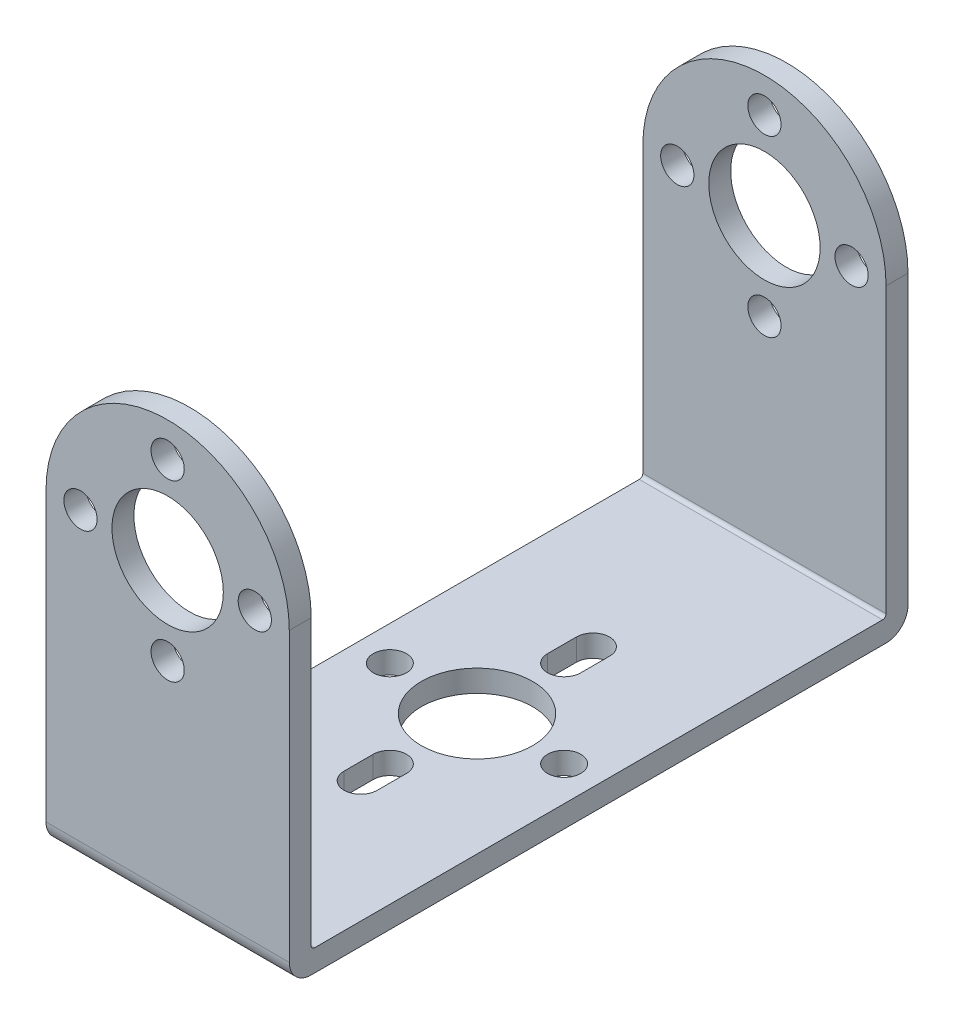
SolidWorks part; units mm, degrees
ref_plane "Front Plane" through (0, 0, 0) normal (0, 0, 1) x (1, 0, 0)
ref_plane "Top Plane" through (0, 0, 0) normal (0, 1, 0) x (1, 0, 0)
ref_plane "Right Plane" through (0, 0, 0) normal (1, 0, 0) x (0, 0, -1)
sketch "Sketch1" plane through (0, 0, 0) normal (1, 0, 0) x (0, 0, -1)
  line L1 (0, 0) -> (44.45, 0)
  line L2 (0, 0) -> (0, 30.9626)
  line L3 (0, 30.9626) -> (44.45, 30.9626)
  line L4 (44.45, 0) -> (44.45, 30.9626)
  dimension "D1" = 30.9626
  dimension "D2" = 44.45
extrude "Extrude1" add sketch "Sketch1" along normal blind 17.4752
sketch "Sketch2" plane through (17.4752, 0, 0) normal (1, 0, 0) x (0, 0, -1)
  line L0 (44.45, 30.9626) -> (0, 30.9626) construction
  line L1 (1.5748, 30.9626) -> (42.8752, 30.9626)
  line L2 (1.5748, 30.9626) -> (1.5748, 1.5748)
  line L3 (1.5748, 1.5748) -> (42.8752, 1.5748)
  line L4 (42.8752, 30.9626) -> (42.8752, 1.5748)
  line L5 (44.45, 0) -> (44.45, 30.9626) construction
  line L6 (0, 0) -> (44.45, 0) construction
  line L7 (0, 30.9626) -> (0, 0) construction
  dimension "D1" = 1.5748
  dimension "D2" = 1.5748
  dimension "D3" = 1.5748
extrude "Extrude2" cut sketch "Sketch2" against normal up to surface (17.4752 mm away) up to face at (0, 15.4813, -22.225)
sketch "Sketch3" plane through (0, 0, 0) normal (0, 0, 1) x (1, 0, 0)
  line L0 (17.4752, 30.9626) -> (0, 30.9626) construction
  line L1 (0, 22.225) -> (0, 0)
  line L2 (0, 0) -> (17.4752, 0)
  line L3 (17.4752, 0) -> (17.4752, 22.225)
  arc A0 (17.4752, 22.225) -> (0, 22.225) centre (8.7376, 22.225) ccw
extrude "Extrude3" cut sketch "Sketch3" against normal through all flip side to cut
sketch "Sketch4" plane through (0, 0, 0) normal (0, 0, 1) x (1, 0, 0)
  circle A0 centre (8.7376, 22.225) radius 4.0005
  circle A1 centre (8.7376, 22.225) radius 6.2611 construction
  circle A2 centre (2.4765, 22.225) radius 1.1938
  circle A3 centre (14.9987, 22.225) radius 1.1938
  circle A4 centre (8.7376, 15.9639) radius 1.1938
  circle A5 centre (8.7376, 28.4861) radius 1.1938
  dimension "D1" = 12.5222
extrude "Extrude4" cut sketch "Sketch4" against normal through all
sketch "Sketch5" plane through (0, 1.5748, 0) normal (0, 1, 0) x (1, 0, 0)
  line L0 (0, 22.225) -> (17.4752, 22.225) construction
  line L1 (0, 1.5748) -> (0, 42.8752) construction
  line L2 (17.4752, 1.5748) -> (17.4752, 42.8752) construction
  line L4 (17.4752, 44.45) -> (0, 44.45) construction
  line L5 (9.9314, 30.5562) -> (9.9314, 28.4861)
  line L6 (7.5438, 30.5562) -> (7.5438, 28.4861)
  line L7 (7.5438, 15.9639) -> (7.5438, 13.8684)
  line L8 (9.9314, 15.9639) -> (9.9314, 13.8684)
  circle A0 centre (8.7376, 22.225) radius 4.0005
  circle A1 centre (8.7376, 22.225) radius 6.2611 construction
  circle A2 centre (2.4765, 22.225) radius 1.1938
  circle A3 centre (14.9987, 22.225) radius 1.1938
  arc A4 (9.9314, 15.9639) -> (7.5438, 15.9639) centre (8.7376, 15.9639) ccw
  arc A5 (7.5438, 28.4861) -> (9.9314, 28.4861) centre (8.7376, 28.4861) ccw
  arc A6 (9.9314, 30.5562) -> (7.5438, 30.5562) centre (8.7376, 30.5562) ccw
  arc A7 (7.5438, 13.8684) -> (9.9314, 13.8684) centre (8.7376, 13.8684) ccw
  point P17 (8.7376, 22.225)
  dimension "D1" = 2.3876
  dimension "D2" = 2.3876
  dimension "D3" = 13.8938
  dimension "D4" = 30.5816
extrude "Extrude5" cut sketch "Sketch5" against normal blind 17.4752
fillet "Fillet1" radius 1.5748 2 edges at (8.7376, 0, -44.45) (8.7376, 0, 0)
fillet "Fillet2" radius 0.254 2 edges at (8.7376, 1.5748, -42.8752) (8.7376, 1.5748, -1.5748)
